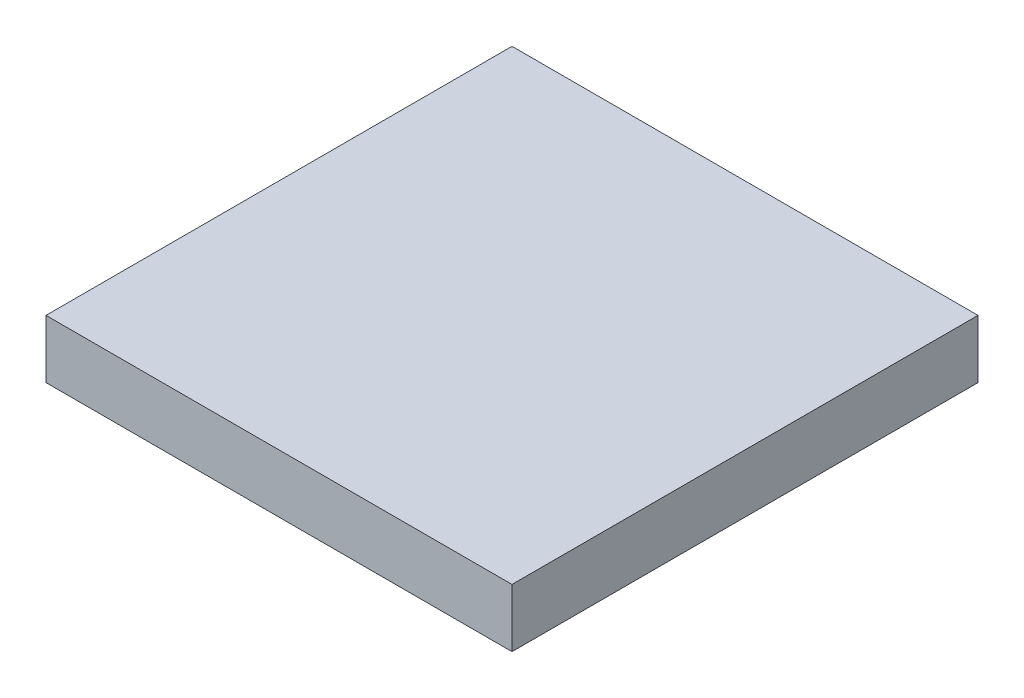
SolidWorks part; units mm, degrees
material "6061 Alloy"
ref_plane "Front Plane" through (0, 0, 0) normal (0, 0, 1) x (1, 0, 0)
ref_plane "Top Plane" through (0, 0, 0) normal (0, 1, 0) x (1, 0, 0)
ref_plane "Right Plane" through (0, 0, 0) normal (1, 0, 0) x (0, 0, -1)
sketch "Sketch1" plane through (0, 0, 0) normal (0, 1, 0) x (1, 0, 0)
  line L1 (-12.7, -12.7) -> (12.7, -12.7)
  line L2 (-12.7, -12.7) -> (-12.7, 12.7)
  line L3 (-12.7, 12.7) -> (12.7, 12.7)
  line L4 (12.7, -12.7) -> (12.7, 12.7)
  line L5 (-12.7, -12.7) -> (12.7, 12.7) construction
  line L6 (-12.7, 12.7) -> (12.7, -12.7) construction
  point P0 (0, 0)
  dimension "D1" = 25.4
  dimension "D2" = 25.4
extrude "Boss-Extrude1" add sketch "Sketch1" along normal blind 3.175
